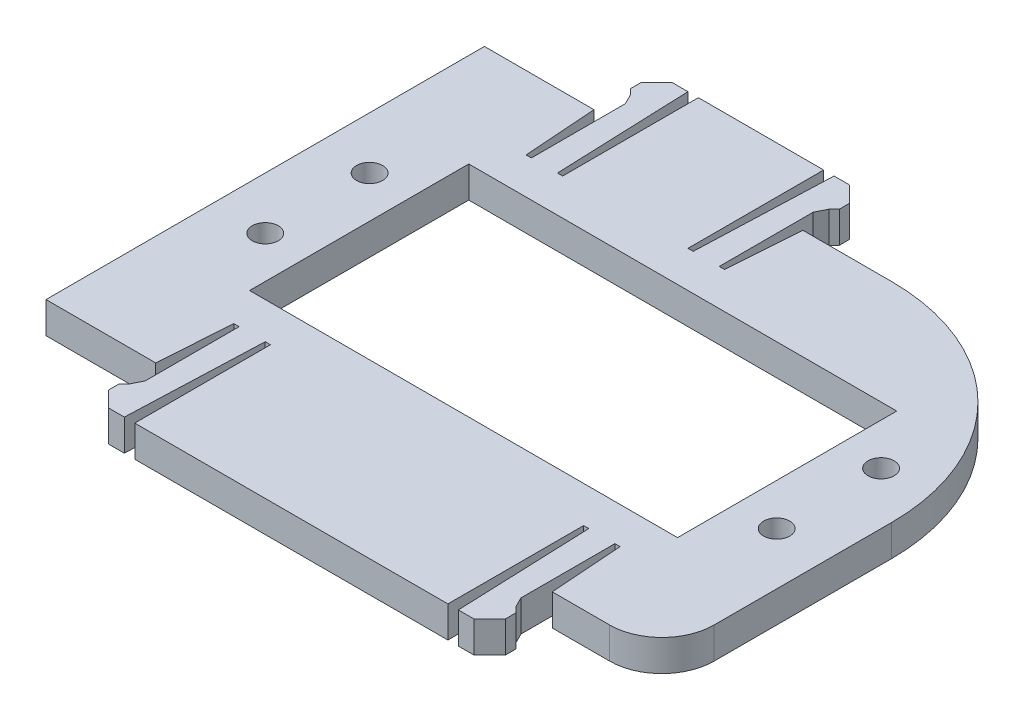
SolidWorks part; units mm, degrees
ref_plane "Front Plane" through (0, 0, 0) normal (0, 0, 1) x (1, 0, 0)
ref_plane "Top Plane" through (0, 0, 0) normal (0, 1, 0) x (1, 0, 0)
ref_plane "Right Plane" through (0, 0, 0) normal (1, 0, 0) x (0, 0, -1)
sketch "Sketch1" plane through (0, 0, 0) normal (0, 1, 0) x (1, 0, 0)
  line L0 (0, 0) -> (-29.9919, 0) construction
  line L1 (19, -21) -> (29.5, -21)
  line L2 (-19, -21) -> (-29.5, -21)
  line L3 (19, -21) -> (18.5, -13.9978)
  line L4 (18.5, -13.9978) -> (18, -13.9978)
  line L5 (18, -13.9978) -> (18, -22.9978)
  line L6 (18, -22.9978) -> (18.5, -23.9978)
  line L7 (-9, 26.9978) -> (-9, 17.1768) construction
  line L8 (-18.5, 13.9978) -> (-18, 13.9978)
  line L9 (-15.5, 13.9978) -> (-15, 13.9978)
  line L10 (-3, 13.9978) -> (-3, 26.9978)
  line L11 (-2, 26.9978) -> (-2.5, 13.9978)
  line L12 (-0.5, 26.9978) -> (-2, 26.9978)
  line L13 (0, 22.3983) -> (0, -22.3983) construction
  line L14 (18.5, -23.9978) -> (19, -24.4978)
  line L15 (19, -24.4978) -> (19, -25.4978)
  line L16 (19, -25.4978) -> (17.5, -26.9978)
  line L17 (17.5, -26.9978) -> (16, -26.9978)
  line L18 (16, -26.9978) -> (15.5, -13.9978)
  line L19 (15.5, -13.9978) -> (15, -13.9978)
  line L20 (15, -13.9978) -> (15, -26.9978)
  line L21 (0, -20.5022) -> (0, -26.2408) construction
  line L22 (-15, -13.9978) -> (-15, -26.9978)
  line L23 (-15.5, -13.9978) -> (-15, -13.9978)
  line L24 (-16, -26.9978) -> (-15.5, -13.9978)
  line L25 (-17.5, -26.9978) -> (-16, -26.9978)
  line L26 (-19, -25.4978) -> (-17.5, -26.9978)
  line L27 (-19, -24.4978) -> (-19, -25.4978)
  line L28 (-18.5, -23.9978) -> (-19, -24.4978)
  line L29 (-18, -22.9978) -> (-18.5, -23.9978)
  line L30 (-18, -13.9978) -> (-18, -22.9978)
  line L31 (-18.5, -13.9978) -> (-18, -13.9978)
  line L32 (-19, -21) -> (-18.5, -13.9978)
  line L33 (15, -26.9978) -> (-15, -26.9978)
  line L34 (1, 25.4978) -> (-0.5, 26.9978)
  line L35 (1, 24.4978) -> (1, 25.4978)
  line L36 (0.5, 23.9978) -> (1, 24.4978)
  line L37 (-3, 26.9978) -> (-15, 26.9978)
  line L38 (-19, 21) -> (-18.5, 13.9978)
  line L39 (0, 22.9978) -> (0.5, 23.9978)
  line L40 (-18, 13.9978) -> (-18, 22.9978)
  line L41 (-18, 22.9978) -> (-18.5, 23.9978)
  line L42 (-18.5, 23.9978) -> (-19, 24.4978)
  line L43 (-19, 24.4978) -> (-19, 25.4978)
  line L44 (-19, 25.4978) -> (-17.5, 26.9978)
  line L45 (-17.5, 26.9978) -> (-16, 26.9978)
  line L46 (-16, 26.9978) -> (-15.5, 13.9978)
  line L47 (0, 13.9978) -> (0, 22.9978)
  line L48 (-15, 13.9978) -> (-15, 26.9978)
  line L49 (1, 21) -> (0.5, 13.9978)
  line L51 (-2.5, 13.9978) -> (-3, 13.9978)
  line L52 (0.5, 13.9978) -> (0, 13.9978)
  line L53 (-19, 21) -> (-29.5, 21)
  line L54 (1, 21) -> (29.5, 21)
  line L62 (-29.5, 21) -> (-29.5, -21)
  line L63 (29.5, 21) -> (29.5, -21)
  point P24 (0, -20.5022)
  point P25 (19, -21)
  point P27 (-8, -20.5022)
  dimension "D5" = 7.0022
  dimension "D3" = 29.5
  dimension "D4" = 18
  dimension "D6" = 7.02
  dimension "D7" = 0.5
  dimension "D8" = 9
  dimension "D9" = 0.5
  dimension "D10" = 7.02
  dimension "D11" = 0.5
  dimension "D12" = 0.5
  dimension "D13" = 9
  dimension "D14" = 0.5
  dimension "D15" = 1
  dimension "D16" = 0.5
  dimension "D17" = 0.5
  dimension "D18" = 1
  dimension "D19" = 1.5
  dimension "D20" = 1.5
  dimension "D21" = 1.5
  dimension "D22" = 0.5
  dimension "D23" = 13
  dimension "D24" = 0.5
  dimension "D25" = 13
  dimension "D26" = 30
  dimension "D27" = 1.118
  dimension "D28" = 0.7071
  dimension "D29" = 0.5
  dimension "D30" = 1
  dimension "D31" = 2.1213
  dimension "D32" = 1.5
  dimension "D33" = 13
  dimension "D34" = 0.5
  dimension "D35" = 0.5
  dimension "D36" = 13
  dimension "D37" = 21
  dimension "D38" = 10.5
  dimension "D39" = 1.5
extrude "Boss-Extrude4" add sketch "Sketch1" along normal blind 3 contours L37 L48 L9 L46 L45 L44 L43 L42 L41 L40 L8 L38 L53 L62 L2 L32 L31 L30 L29 L28 L27 L26 L25 L24 L23 L22 L33 L20 L19 L18 L17 L16 L15 L14 L6 L5 L4 L3 L1 L63 L54 L49 L52 L47 L39 L36 L35 L34 L12 L11 L51 L10
sketch "Sketch7" plane through (0, 3, 0) normal (0, 1, 0) x (1, 0, 0)
  point P0 (0, 0)
  line B0 (-20.5, -10.5) -> (20.5, -10.5)
  line B1 (-20.5, -10.5) -> (-20.5, 10.5)
  line B2 (-20.5, 10.5) -> (20.5, 10.5)
  line B3 (20.5, -10.5) -> (20.5, 10.5)
  line B4 (-20.5, -10.5) -> (20.5, 10.5) construction
  line B5 (-20.5, 10.5) -> (20.5, -10.5) construction
  circle B6 centre (-24.5, 5) radius 1.25
  circle B7 centre (-24.5, -5) radius 1.25
  circle B8 centre (24.5, -5) radius 1.25
  circle B9 centre (24.5, 5) radius 1.25
sketch_block_instance "Block5-1"
sketch_block "Block5" parameters "D2"=2.5, "D1"=4
extrude "Cut-Extrude1" cut sketch "Sketch7" against normal blind 3
fillet "Fillet2" radius 20 1 edges at (29.5, 1.5, -21)
fillet "Fillet3" radius 5 1 edges at (29.5, 1.5, 21)
sketch "Sketch8" plane through (0, 3, 0) normal (0, 1, 0) x (1, 0, 0)
  text T0 "Ba" font "Century Gothic" height in points 20
  dimension "D1" = 18.3071
  dimension "D2" = 5.5
